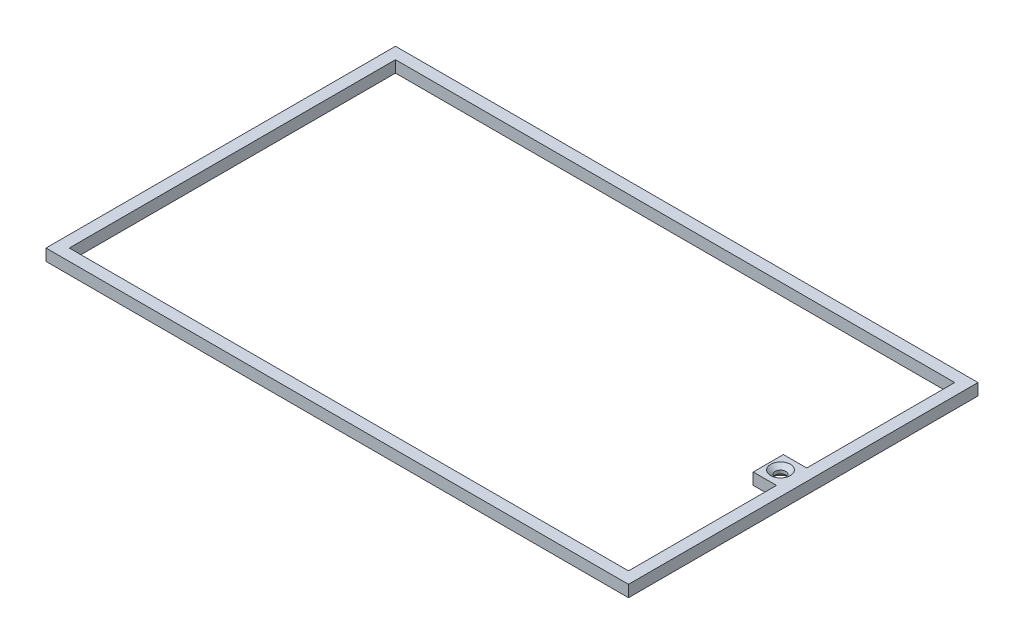
SolidWorks part; units mm, degrees
ref_plane "Front Plane" through (0, 0, 0) normal (0, 0, 1) x (1, 0, 0)
ref_plane "Top Plane" through (0, 0, 0) normal (0, 1, 0) x (1, 0, 0)
ref_plane "Right Plane" through (0, 0, 0) normal (1, 0, 0) x (0, 0, -1)
sketch "Sketch1" plane through (0, 0, 0) normal (0, 1, 0) x (1, 0, 0)
  line L1 (0, 0) -> (250, 0)
  line L2 (0, 0) -> (0, 150)
  line L3 (0, 150) -> (250, 150)
  line L4 (250, 0) -> (250, 150)
extrude "Boss-Extrude1" add sketch "Sketch1" along normal blind 5
sketch "Sketch2" plane through (0, 5, 0) normal (0, 1, 0) x (1, 0, 0)
  line L0 (250, 0) -> (250, 150) construction
  line L1 (5, 5) -> (245, 5)
  line L2 (5, 5) -> (5, 145)
  line L3 (5, 145) -> (245, 145)
  line L4 (245, 5) -> (245, 68.5227)
  line L6 (235, 81.4773) -> (245, 81.4773)
  line L8 (235, 81.4773) -> (235, 68.5227)
  line L10 (235, 68.5227) -> (245, 68.5227)
  line L12 (245, 81.4773) -> (245, 145)
  line L13 (235, 81.4773) -> (250, 71.7614) construction
  line L14 (235, 68.5227) -> (245, 75) construction
  point P4 (245, 75)
extrude "Cut-Extrude1" cut sketch "Sketch2" against normal blind 5
hole_wizard "CSK for #8 Flat Head Machine Screw (100)1" positions "3DSketch1" profile "Sketch3" countersink size "#8" standard "ANSI Inch" end condition through all
sketch3d "3DSketch1"
  point P0 (240.1109, 5, -75.136)
  point P3 (240.1109, 5, -75.136)
sketch "Sketch3" plane through (240.1109, 5, -75.136) normal (1, 0, 0) x (0, 0, 1)
  line L0 (0, 0) -> (0, 5)
  line L1 (0, 5) -> (2.2479, 5)
  line L2 (2.2479, 5) -> (2.2479, 1.6518)
  line L3 (2.2479, 1.6518) -> (4.2164, 0)
  line L5 (4.2164, 0) -> (0, 0)
  line L6 (-2.2479, 1.6518) -> (-4.2164, 0) construction
  line L11 (0, -6.35) -> (0, 107.95) construction
  dimension "Thru Hole Dia." = 4.4958
  dimension "Thru Hole Depth" = 5
  dimension "Near C'Sink Dia." = 8.4328
  dimension "Near C'Sink Angle" = 100
chamfer "Chamfer1" distance 2 angle 45 1 edges at (240.1109, 0, -72.8881)
